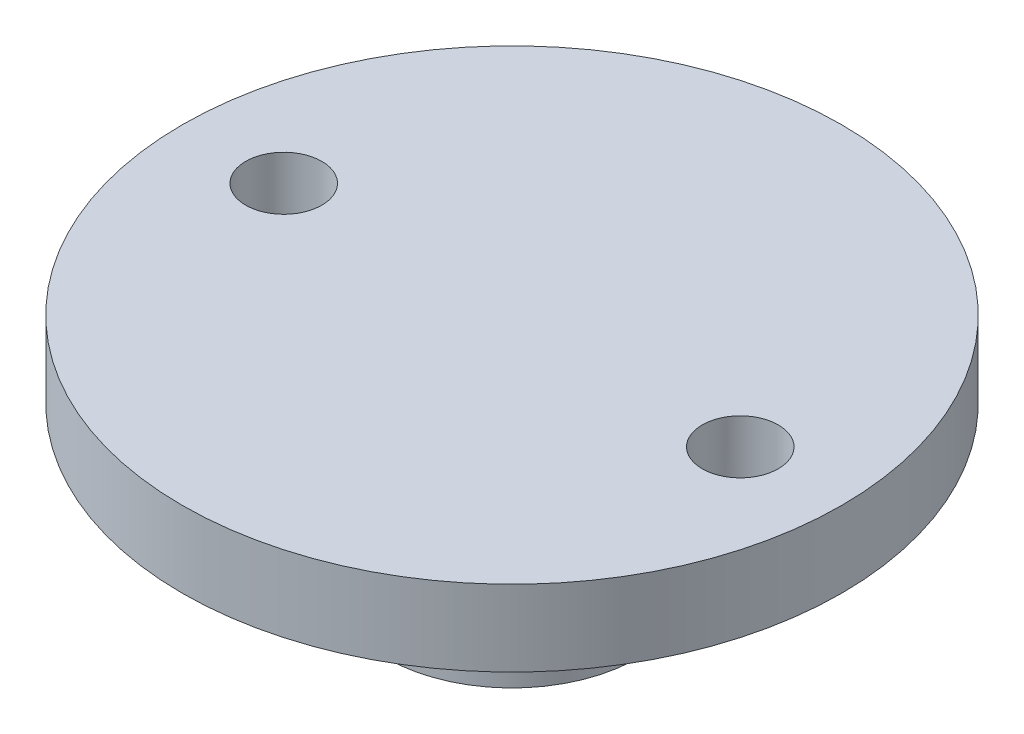
SolidWorks part; units mm, degrees
material "1060 Alloy"
ref_plane "Front Plane" through (0, 0, 0) normal (0, 0, 1) x (1, 0, 0)
ref_plane "Top Plane" through (0, 0, 0) normal (0, 1, 0) x (1, 0, 0)
ref_plane "Right Plane" through (0, 0, 0) normal (1, 0, 0) x (0, 0, -1)
sketch "Sketch1" plane through (0, 0, 0) normal (0, 0, 1) x (1, 0, 0)
  line L0 (0, 0) -> (0, 50000) construction
  line L3 (13, 0) -> (13, -3)
  line L4 (13, -3) -> (5, -3)
  line L5 (5, -3) -> (5, -9.2)
  line L6 (5, -9.2) -> (3, -9.2)
  line L7 (0, -6.2) -> (0, 0)
  line L8 (0, 0) -> (13, 0)
  line L9 (9, -3) -> (9, 0) construction
  line L10 (55, 0) -> (-55, 0) construction
  line L11 (3, -9.2) -> (3, -6.2)
  line L12 (3, -6.2) -> (0, -6.2)
  dimension "D1" = 26
  dimension "D2" = 10
  dimension "D3" = 3
  dimension "D4" = 9
  dimension "D5" = 6.2
  dimension "D6" = 3
  dimension "D7" = 3
revolve "Revolve1" add sketch "Sketch1" angle 360 about L0
sketch "Sketch2" plane through (0, 0, 0) normal (0, 1, 0) x (1, 0, 0)
  line L0 (0, 13) -> (0, -13) construction
  line L1 (0, -5.06) -> (0, 5.06) construction
  circle A0 centre (9, 0) radius 1.5
  circle A1 centre (0, 0) radius 13 construction
  circle A2 centre (-9, 0) radius 1.5
  dimension "D1" = 3
extrude "Cut-Extrude1" cut sketch "Sketch2" against normal through all
